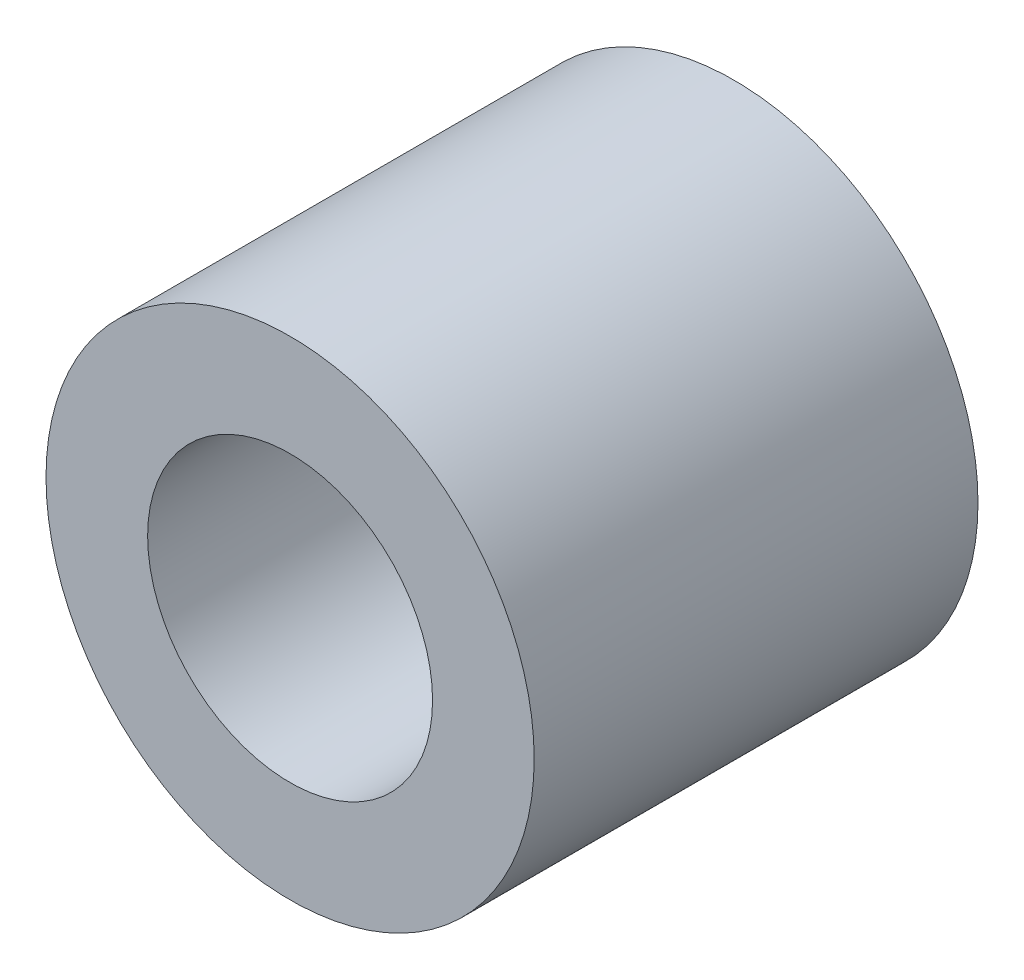
SolidWorks part; units mm, degrees
ref_plane "Plan de face" through (0, 0, 0) normal (0, 0, 1) x (1, 0, 0)
ref_plane "Plan de dessus" through (0, 0, 0) normal (0, 1, 0) x (1, 0, 0)
ref_plane "Plan de droite" through (0, 0, 0) normal (1, 0, 0) x (0, 0, -1)
sketch "Esquisse1" plane through (0, 0, 0) normal (0, 0, 1) x (1, 0, 0)
  circle A0 centre (0, 0) radius 27.5
  dimension "D1" = 55
extrude "Boss.-Extru.1" add sketch "Esquisse1" along normal blind 20
sketch "Esquisse2" plane through (0, 0, 0) normal (0, 0, 1) x (1, 0, 0)
  circle A0 centre (0, 0) radius 27.5
  dimension "D1" = 55
extrude "Boss.-Extru.2" add sketch "Esquisse2" along normal blind 50
sketch "Esquisse3" plane through (0, 0, 0) normal (0, 0, -1) x (-1, 0, 0)
  circle A0 centre (0, 0) radius 16.05
  dimension "D1" = 32.1
extrude "Enlèv. mat.-Extru.1" cut sketch "Esquisse3" against normal through all
